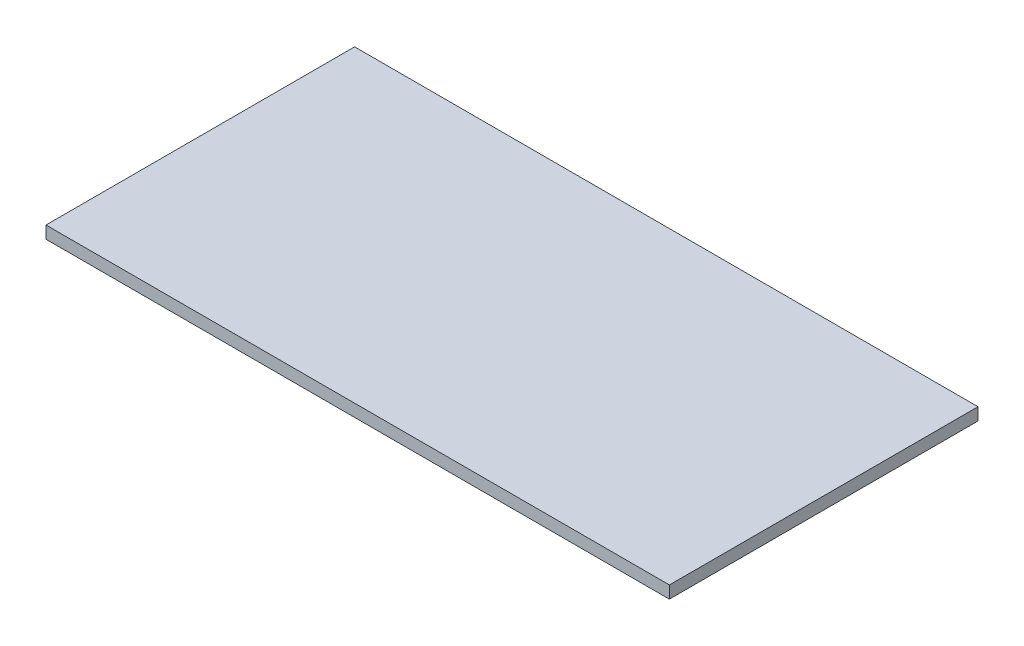
SolidWorks part; units mm, degrees
ref_plane "Front Plane" through (0, 0, 0) normal (0, 0, 1) x (1, 0, 0)
ref_plane "Top Plane" through (0, 0, 0) normal (0, 1, 0) x (1, 0, 0)
ref_plane "Right Plane" through (0, 0, 0) normal (1, 0, 0) x (0, 0, -1)
sketch "Sketch1" plane through (0, 0, 0) normal (0, 1, 0) x (1, 0, 0)
  line L1 (-320.675, -158.75) -> (320.675, -158.75)
  line L2 (-320.675, -158.75) -> (-320.675, 158.75)
  line L3 (-320.675, 158.75) -> (320.675, 158.75)
  line L4 (320.675, -158.75) -> (320.675, 158.75)
  line L5 (-320.675, -158.75) -> (320.675, 158.75) construction
  line L6 (-320.675, 158.75) -> (320.675, -158.75) construction
  point P0 (0, 0)
  dimension "D1" = 641.35
  dimension "D2" = 317.5
extrude "Boss-Extrude1" add sketch "Sketch1" along normal blind 12.7
